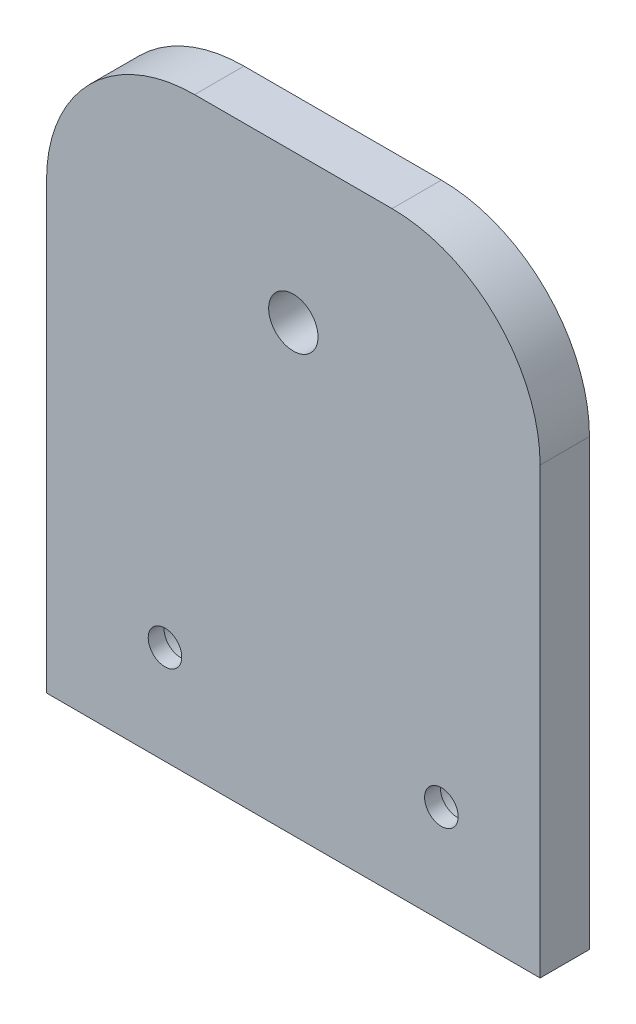
SolidWorks part; units mm, degrees
material "Allzweck-PBT"
ref_plane "Ebene vorne" through (0, 0, 0) normal (0, 0, 1) x (1, 0, 0)
ref_plane "Ebene oben" through (0, 0, 0) normal (0, 1, 0) x (1, 0, 0)
ref_plane "Ebene rechts" through (0, 0, 0) normal (1, 0, 0) x (0, 0, -1)
sketch "Skizze1" plane through (0, 0, 0) normal (0, 0, 1) x (1, 0, 0)
  line L1 (0, 0) -> (50, 0)
  line L2 (0, 0) -> (0, 45)
  line L3 (15, 60) -> (35, 60)
  line L4 (50, 0) -> (50, 45)
  arc A0 (0, 45) -> (15, 60) centre (15, 45) cw
  arc A1 (35, 60) -> (50, 45) centre (35, 45) cw
  circle A2 centre (25, 45) radius 2.5
  point P7 (0, 60)
  point P10 (50, 60)
  dimension "D3" = 15
  dimension "D4" = 5
  dimension "D1" = 60
  dimension "D2" = 50
  dimension "D5" = 10
extrude "Aufsatz-Linear austragen1" add sketch "Skizze1" along normal blind 5
hole_wizard "Stirnsenkung für M3 Zylinderschraube mit Innensechskant2" positions "Skizze6" profile "Skizze7" counterbore size "M3" standard "DIN" end condition through all
sketch "Skizze6" plane through (0, 0, 0) normal (0, 0, -1) x (-1, 0, 0)
  line L0 (-50, 0) -> (-50, 45) construction
  line L3 (0, 0) -> (-50, 0) construction
  line L4 (0, 45) -> (0, 0) construction
  point P0 (-40, 10)
  point P2 (-12, 10)
  dimension "D1" = 10
  dimension "D2" = 10
  dimension "D3" = 10
  dimension "D4" = 12
sketch "Skizze7" plane through (40, 10, 0) normal (1, 0, 0) x (0, 1, 0)
  line L0 (0, 0) -> (0, 5)
  line L1 (0, 5) -> (1.7, 5)
  line L3 (1.7, 5) -> (1.7, 3.4)
  line L4 (1.7, 3.4) -> (3.25, 3.4)
  line L5 (3.25, 3.4) -> (3.25, 0)
  line L7 (3.25, 0) -> (0, 0)
  line L11 (0, -6.35) -> (0, 107.95) construction
  dimension "Bohrerdurchmesser" = 3.4
  dimension "Bohrungstiefe" = 5
  dimension "Senkdurchmesser2" = 6.5
  dimension "Senktiefe2" = 3.4
